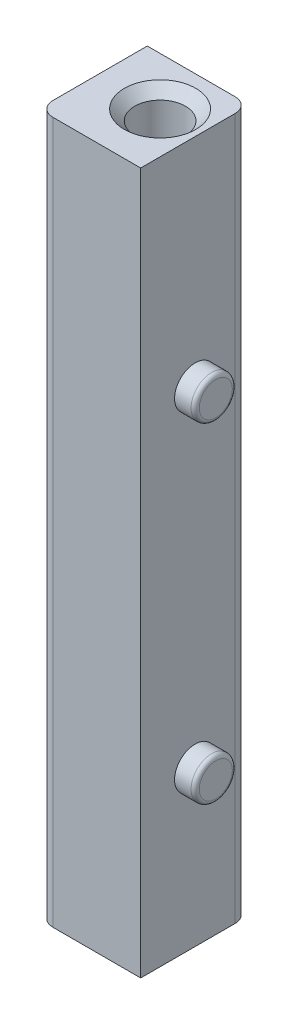
SolidWorks part; units mm, degrees
material "ABS"
ref_plane "Front Plane" through (0, 0, 0) normal (0, 0, 1) x (1, 0, 0)
ref_plane "Top Plane" through (0, 0, 0) normal (0, 1, 0) x (1, 0, 0)
ref_plane "Right Plane" through (0, 0, 0) normal (1, 0, 0) x (0, 0, -1)
sketch "Sketch1" plane through (0, 0, 0) normal (0, 1, 0) x (1, 0, 0)
  line L1 (-7.493, 5.9182) -> (5.1054, 5.9182)
  line L2 (-7.493, 5.9182) -> (-7.493, -7.493)
  line L3 (-7.493, -7.493) -> (5.1054, -7.493)
  line L4 (5.1054, 5.9182) -> (5.1054, -7.493)
  dimension "D1" = 13.4112
  dimension "D2" = 12.5984
  dimension "D3" = 5.9182
  dimension "D4" = 5.1054
extrude "Boss-Extrude1" add sketch "Sketch1" along normal blind 46.99 and the other way blind 39.37
sketch "Sketch2" plane through (0, 46.99, 0) normal (0, 1, 0) x (1, 0, 0)
  circle A0 centre (0, 0) radius 3.1242
  dimension "D1" = 6.2484
extrude "Cut-Extrude1" cut sketch "Sketch2" against normal through all
sketch "Sketch4" plane through (5.1054, 0, 0) normal (1, 0, 0) x (0, 0, -1)
  line L0 (0, 0) -> (-6.723, 0) construction
  line L1 (-0.7874, -39.37) -> (-0.7874, -45.321) construction
  line L2 (-7.493, -39.37) -> (5.9182, -39.37) construction
  circle A0 centre (-0.7874, -20.32) radius 2.54
  dimension "D1" = 5.08
  dimension "D2" = 20.32
extrude "Boss-Extrude2" add sketch "Sketch4" along normal blind 2.54
fillet "Fillet2" radius 0.508 1 edges at (7.6454, -20.32, -1.7526)
mirror "Mirror1" about plane through (0, 0, 0) normal (0, 1, 0) of "Fillet2", "Boss-Extrude2"
fillet "Fillet1" radius 1.778 2 edges at (-7.493, 3.81, 7.493) (5.1054, 3.81, -5.9182)
chamfer "Chamfer1" distance 1.27 angle 45 1 edges at (0, 46.99, 3.1242)
